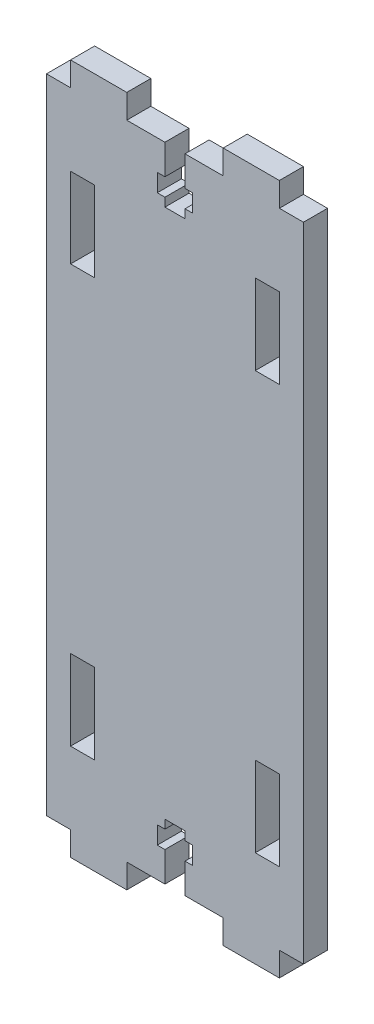
SolidWorks part; units mm, degrees
ref_plane "정면" through (0, 0, 0) normal (0, 0, 1) x (1, 0, 0)
ref_plane "윗면" through (0, 0, 0) normal (0, 1, 0) x (1, 0, 0)
ref_plane "우측면" through (0, 0, 0) normal (1, 0, 0) x (0, 0, -1)
sketch "스케치1" plane through (0, 0, 0) normal (0, 0, 1) x (1, 0, 0)
  line L1 (0, 0) -> (32, 0)
  line L2 (0, 0) -> (0, 86)
  line L3 (0, 86) -> (32, 86)
  line L4 (32, 0) -> (32, 86)
  dimension "D1" = 32
  dimension "D2" = 86
extrude "보스-돌출1" add sketch "스케치1" along normal blind 3
sketch "스케치2" plane through (0, 0, 3) normal (0, 0, 1) x (1, 0, 0)
  line L0 (32, 0) -> (32, 86) construction
  line L1 (0, 0) -> (32, 0)
  line L2 (0, 0) -> (0, 3)
  line L3 (0, 3) -> (3, 3)
  line L4 (32, 0) -> (32, 3)
  line L5 (10, 3) -> (22, 3)
  line L7 (3, 3) -> (3, 0)
  line L8 (3, 0) -> (10, 0)
  line L9 (10, 3) -> (10, 0)
  line L11 (22, 3) -> (22, 0)
  line L12 (22, 0) -> (29, 0)
  line L13 (29, 3) -> (29, 0)
  line L14 (29, 3) -> (32, 3)
  line L15 (-8.1831, 43) -> (37.0217, 43) construction
  line L16 (29, 83) -> (32, 83)
  line L17 (29, 83) -> (29, 86)
  line L18 (22, 83) -> (22, 86)
  line L19 (10, 83) -> (22, 83)
  line L20 (10, 83) -> (10, 86)
  line L21 (3, 83) -> (3, 86)
  line L22 (0, 86) -> (32, 86)
  line L23 (0, 86) -> (0, 83)
  line L24 (0, 83) -> (3, 83)
  line M9 (0, 86) -> (0, 0)
  line M10 (0, 0) -> (32, 0)
  line M11 (32, 0) -> (32, 86)
  line M12 (32, 86) -> (0, 86)
  dimension "D1" = 3
  dimension "D2" = 3
  dimension "D3" = 7
  dimension "D4" = 3
  dimension "D5" = 7
extrude "컷-돌출1" cut sketch "스케치2" against normal through all contours L20 L19 L18 M12 | L24 L21 M9 M12 | L17 L16 M11 M12 | L11 L5 L9 M10 | L7 L3 M9 M10 | L14 L13 M10 M11
sketch "스케치3" plane through (0, 0, 3) normal (0, 0, 1) x (1, 0, 0)
  line L0 (-10.6743, 43) -> (41.9059, 43) construction
  line L1 (29, 74) -> (26, 74)
  line L2 (29, 74) -> (29, 64)
  line L3 (29, 64) -> (26, 64)
  line L4 (26, 74) -> (26, 64)
  line L6 (16, 88.7196) -> (16, -3.1587) construction
  line L7 (3, 64) -> (6, 64)
  line L8 (6, 74) -> (6, 64)
  line L9 (3, 74) -> (6, 74)
  line L10 (3, 74) -> (3, 64)
  line L11 (29, 22) -> (26, 22)
  line L12 (26, 12) -> (26, 22)
  line L13 (29, 12) -> (26, 12)
  line L14 (29, 12) -> (29, 22)
  line L15 (3, 12) -> (3, 22)
  line L16 (3, 12) -> (6, 12)
  line L17 (6, 12) -> (6, 22)
  line L18 (3, 22) -> (6, 22)
  dimension "D1" = 3
  dimension "D2" = 9
  dimension "D3" = 10
extrude "컷-돌출2" cut sketch "스케치3" against normal through all
sketch "스케치4" plane through (0, 0, 3) normal (0, 0, 1) x (1, 0, 0)
  line L0 (10, 3) -> (22, 3) construction
  line L1 (14.75, 3) -> (17.25, 3)
  line L2 (14.75, 3) -> (14.75, 6.7278)
  line L3 (14.75, 10) -> (17.25, 10)
  line L4 (17.25, 3) -> (17.25, 6.7278)
  line L5 (14.75, 8.9278) -> (14.75, 10)
  line L6 (0, 83) -> (0, 3) construction
  line L7 (17.25, 8.9278) -> (18.2, 8.9278)
  line L8 (13.8, 8.9278) -> (14.75, 8.9278)
  line L9 (13.8, 8.9278) -> (13.8, 6.7278)
  line L10 (13.8, 6.7278) -> (14.75, 6.7278)
  line L11 (18.2, 8.9278) -> (18.2, 6.7278)
  line L12 (17.25, 8.9278) -> (17.25, 10)
  line L13 (17.25, 6.7278) -> (18.2, 6.7278)
  line L14 (-7.5495, 43) -> (43.2573, 43) construction
  line L15 (13.8, 77.0722) -> (14.75, 77.0722)
  line L16 (14.75, 77.0722) -> (14.75, 76)
  line L17 (14.75, 76) -> (17.25, 76)
  line L18 (17.25, 77.0722) -> (17.25, 76)
  line L19 (17.25, 77.0722) -> (18.2, 77.0722)
  line L20 (18.2, 77.0722) -> (18.2, 79.2722)
  line L21 (17.25, 79.2722) -> (18.2, 79.2722)
  line L22 (17.25, 83) -> (17.25, 79.2722)
  line L23 (14.75, 83) -> (17.25, 83)
  line L24 (14.75, 83) -> (14.75, 79.2722)
  line L25 (13.8, 79.2722) -> (14.75, 79.2722)
  line L26 (13.8, 77.0722) -> (13.8, 79.2722)
  dimension "D1" = 7
  dimension "D2" = 2.5
  dimension "D3" = 14.75
  dimension "D4" = 4.4
  dimension "D5" = 2.2
  dimension "D6" = 13.8
extrude "컷-돌출3" cut sketch "스케치4" against normal blind 10
